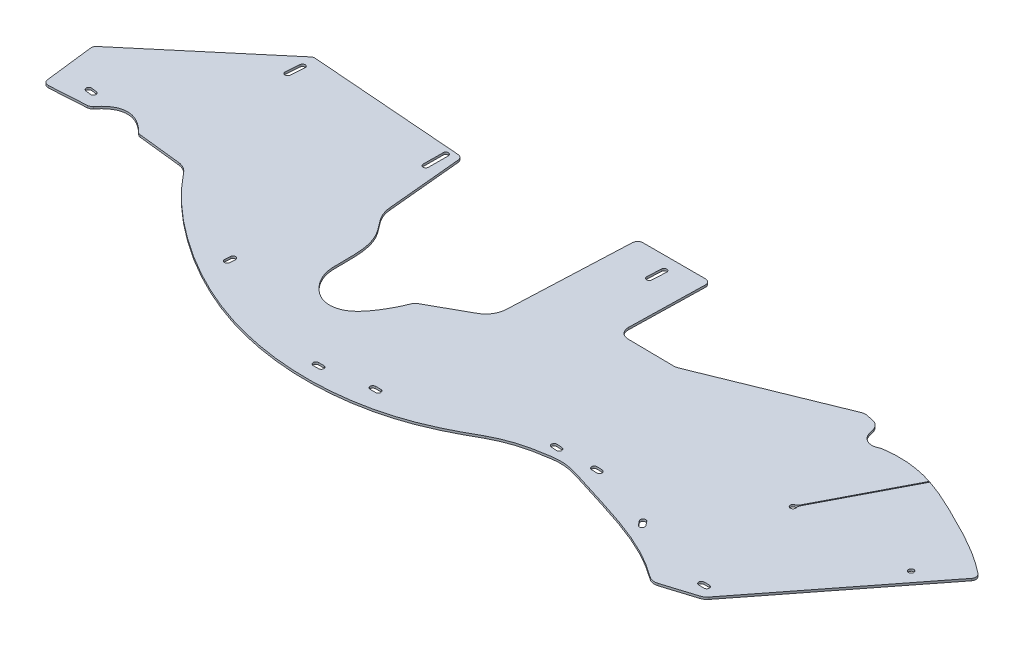
SolidWorks part; units mm, degrees
ref_plane "Front Plane" through (0, 0, 0) normal (0, 0, 1) x (1, 0, 0)
ref_plane "Top Plane" through (0, 0, 0) normal (0, 1, 0) x (1, 0, 0)
ref_plane "Right Plane" through (0, 0, 0) normal (1, 0, 0) x (0, 0, -1)
sketch "Sketch1" plane through (0, 0, 0) normal (0, 1, 0) x (1, 0, 0)
  line L0 (851.3584, -690.9266) -> (2338.9033, -2006.5335) construction
  line L1 (0, 0) -> (914.4, 0)
  line L2 (-5.3287, -153.1342) -> (131.8706, -37.3515)
  line L3 (136.4536, -35.8731) -> (319.5901, -49.9793)
  line L4 (325.4241, -55.712) -> (333.8869, -145.0824)
  line L5 (341.0028, -163.6309) -> (350.751, -176.7721)
  line L6 (-7.538, -158.7449) -> (-0.5962, -216.4972)
  line L7 (6.1047, -222.077) -> (49.5173, -219.3625)
  line L8 (111.0954, -218.2411) -> (162.3658, -223.8905)
  line L9 (878.7809, -371.8765) -> (916.7447, -360.0034)
  line L10 (922.964, -355.6982) -> (1059.3899, -180.9691)
  line L11 (600.276, -37.4685) -> (598.3017, -126.5968)
  line L12 (610.0599, -138.7632) -> (664.7501, -139.4182)
  line L13 (669.6781, -138.4869) -> (823.2965, -76.141)
  line L14 (830.7465, -75.4935) -> (838.6732, -77.2008)
  line L15 (848.1714, -85.9934) -> (850.3383, -93.2741)
  line L16 (448.4134, -227.3098) -> (494.4029, -201.6417)
  line L17 (507.4001, -180.5648) -> (513.6347, -37.0522)
  line L18 (519.9787, -30.9778) -> (593.9275, -30.9778)
  line L19 (34.0126, -202.2038) -> (40.3015, -203.0832) construction
  line L20 (34.4523, -199.0594) -> (40.7411, -199.9388)
  line L21 (33.573, -205.3482) -> (39.8618, -206.2276)
  line L22 (135.4768, -67.9225) -> (136.7875, -51.6134) construction
  line L23 (132.312, -67.6682) -> (133.6227, -51.359)
  line L24 (138.6416, -68.1769) -> (139.9523, -51.8677)
  line L25 (312.1521, -57.0309) -> (312.0105, -80.6873) construction
  line L26 (315.3271, -57.0499) -> (315.1854, -80.7063)
  line L27 (308.9772, -57.0118) -> (308.8355, -80.6683)
  line L28 (292.1635, -296.2194) -> (292.6086, -289.885) construction
  line L29 (288.9963, -295.9968) -> (289.4414, -289.6625)
  line L30 (295.3307, -296.4419) -> (295.7758, -290.1075)
  line L31 (450.5431, -349.5399) -> (456.8931, -349.5401) construction
  line L32 (450.5432, -346.3649) -> (456.8932, -346.3651)
  line L33 (450.5431, -352.7149) -> (456.8931, -352.7151)
  line L34 (508.8141, -340.1517) -> (515.1641, -340.1517) construction
  line L35 (508.8141, -336.9767) -> (515.1641, -336.9767)
  line L36 (508.8141, -343.3267) -> (515.1641, -343.3267)
  line L37 (675.6954, -292.0677) -> (682.0278, -292.54) construction
  line L38 (675.9315, -288.9015) -> (682.2639, -289.3738)
  line L39 (675.4592, -295.2339) -> (681.7916, -295.7062)
  line L40 (722.662, -291.3716) -> (729.0031, -291.7069) construction
  line L41 (722.8296, -288.201) -> (729.1708, -288.5363)
  line L42 (722.4943, -294.5422) -> (728.8355, -294.8775)
  line L43 (805.8956, -316.7947) -> (809.8059, -321.7979) construction
  line L44 (808.3972, -314.8396) -> (812.3075, -319.8428)
  line L45 (803.394, -318.7499) -> (807.3043, -323.7531)
  line L46 (904.6062, -346.3649) -> (910.9562, -346.3649) construction
  line L47 (904.6062, -343.1899) -> (910.9562, -343.1899)
  line L48 (904.6062, -349.5399) -> (910.9562, -349.5399)
  line L49 (560.224, -63.7474) -> (561.1068, -47.0434) construction
  line L50 (557.0534, -63.5799) -> (557.9362, -46.8758)
  line L51 (563.3946, -63.915) -> (564.2773, -47.2109)
  line L52 (883.5758, -207.7343) -> (935.9714, -106.7485)
  line L53 (882.6157, -206.9681) -> (934.8092, -106.372)
  line L54 (881.008, -210.0666) -> (882.0579, -210.6598) construction
  line L55 (881.5329, -210.3632) -> (879.9994, -213.0771) construction
  arc A1 (850.3383, -93.2741) -> (870.1301, -101.8845) centre (863.8577, -89.2504) ccw
  arc A2 (175.2485, -231.0039) -> (162.3658, -223.8905) centre (160.2703, -242.9077) ccw
  arc A3 (333.8869, -145.0824) -> (341.0028, -163.6309) centre (370.7079, -141.5956) ccw
  arc A4 (494.4029, -201.6417) -> (507.4001, -180.5648) centre (482.024, -179.4624) ccw
  arc A5 (598.3017, -126.5968) -> (610.0599, -138.7632) centre (610.2025, -126.8604) ccw
  arc A6 (664.7501, -139.4182) -> (669.6781, -138.4869) centre (664.9022, -126.7191) ccw
  arc A7 (878.7809, -371.8765) -> (867.4226, -369.9547) centre (874.99, -359.7554) cw
  arc A8 (916.7447, -360.0034) -> (922.964, -355.6982) centre (912.9538, -347.8824) ccw
  arc A9 (873.7509, -100.7225) -> (870.1301, -101.8845) centre (875.7775, -113.2598) ccw
  arc A10 (823.2965, -76.141) -> (830.7465, -75.4935) centre (828.0725, -87.9088) cw
  arc A11 (838.6732, -77.2008) -> (848.1714, -85.9934) centre (835.9991, -89.6161) cw
  arc A12 (1059.3899, -180.9691) -> (1058.3506, -172.1019) centre (1054.3849, -177.0612) ccw
  arc A13 (34.4523, -199.0594) -> (33.573, -205.3482) centre (34.0126, -202.2038) ccw
  arc A14 (39.8618, -206.2276) -> (40.7411, -199.9388) centre (40.3015, -203.0832) ccw
  arc A15 (132.312, -67.6682) -> (138.6416, -68.1769) centre (135.4768, -67.9225) ccw
  arc A16 (139.9523, -51.8677) -> (133.6227, -51.359) centre (136.7875, -51.6134) ccw
  arc A17 (315.3271, -57.0499) -> (308.9772, -57.0118) centre (312.1521, -57.0309) ccw
  arc A18 (308.8355, -80.6683) -> (315.1854, -80.7063) centre (312.0105, -80.6873) ccw
  arc A19 (288.9963, -295.9968) -> (295.3307, -296.4419) centre (292.1635, -296.2194) ccw
  arc A20 (295.7758, -290.1075) -> (289.4414, -289.6625) centre (292.6086, -289.885) ccw
  arc A21 (450.5432, -346.3649) -> (450.5431, -352.7149) centre (450.5431, -349.5399) ccw
  arc A22 (456.8931, -352.7151) -> (456.8932, -346.3651) centre (456.8931, -349.5401) ccw
  arc A23 (508.8141, -336.9767) -> (508.8141, -343.3267) centre (508.8141, -340.1517) ccw
  arc A24 (515.1641, -343.3267) -> (515.1641, -336.9767) centre (515.1641, -340.1517) ccw
  arc A25 (675.9315, -288.9015) -> (675.4592, -295.2339) centre (675.6954, -292.0677) ccw
  arc A26 (681.7916, -295.7062) -> (682.2639, -289.3738) centre (682.0278, -292.54) ccw
  arc A27 (722.8296, -288.201) -> (722.4943, -294.5422) centre (722.662, -291.3716) ccw
  arc A28 (728.8355, -294.8775) -> (729.1708, -288.5363) centre (729.0031, -291.7069) ccw
  arc A29 (808.3972, -314.8396) -> (803.394, -318.7499) centre (805.8956, -316.7947) ccw
  arc A30 (807.3043, -323.7531) -> (812.3075, -319.8428) centre (809.8059, -321.7979) ccw
  arc A31 (904.6062, -343.1899) -> (904.6062, -349.5399) centre (904.6062, -346.3649) ccw
  arc A32 (910.9562, -349.5399) -> (910.9562, -343.1899) centre (910.9562, -346.3649) ccw
  arc A33 (557.0534, -63.5799) -> (563.3946, -63.915) centre (560.224, -63.7474) ccw
  arc A34 (564.2773, -47.2109) -> (557.9362, -46.8758) centre (561.1068, -47.0434) ccw
  arc A35 (878.9926, -210.066) -> (883.0703, -212.271) centre (879.9994, -213.0771) ccw
  circle A36 centre (1016.0848, -209.0617) radius 3.175
  arc A37 (600.276, -37.4685) -> (593.9275, -30.9778) centre (593.9275, -37.3278) ccw
  arc A38 (513.6347, -37.0522) -> (519.9787, -30.9778) centre (519.9787, -37.3278) cw
  arc A39 (445.65, -230.4044) -> (448.4134, -227.3098) centre (451.5082, -232.8547) cw
  arc A40 (319.5901, -49.9793) -> (325.4241, -55.712) centre (319.1024, -56.3106) cw
  arc A41 (107.2877, -216.4064) -> (111.0954, -218.2411) centre (111.7908, -211.9293) ccw
  arc A42 (49.5173, -219.3625) -> (54.0607, -217.0152) centre (49.121, -213.0249) ccw
  arc A43 (-0.5962, -216.4972) -> (6.1047, -222.077) centre (5.7085, -215.7393) ccw
  arc A44 (-5.3287, -153.1342) -> (-7.538, -158.7449) centre (-1.2334, -157.9871) ccw
  arc A45 (131.8706, -37.3515) -> (136.4536, -35.8731) centre (135.9659, -42.2043) cw
  arc A46 (883.5758, -207.7343) -> (883.0703, -212.271) centre (889.2123, -210.6587) ccw
  arc A47 (882.6157, -206.9681) -> (878.9926, -210.066) centre (876.9792, -204.0436) cw
  spline S0 degree 3 poles (54.0607, -217.0152) (61.5062, -207.798) (70.9402, -202.0115) (88.8144, -201.9633) (99.0041, -208.0746) (107.2877, -216.4064) knots 0.031006 0.031006 0.031006 0.031006 0.441036 0.535227 0.972916 0.972916 0.972916 0.972916
  spline S1 degree 3 poles (873.7509, -100.7225) (892.0964, -97.7569) (912.9126, -99.7984) (932.4884, -105.6288) (934.8092, -106.372) knots 0.010512 0.010512 0.010512 0.010512 0.267872 0.302747 0.302747 0.302747 0.302747
  spline S2 degree 3 poles (867.4226, -369.9547) (846.2872, -354.2729) (800.4442, -332.5321) (742.2536, -316.1537) (700.4667, -302.0566) (673.1755, -306.5267) (649.18, -311.739) (630.6651, -319.7057) (625.0304, -322.9406) knots 0.023196 0.023196 0.023196 0.023196 0.311711 0.603247 0.708401 0.803326 0.906876 1 1 1 1
  spline S3 degree 3 poles (350.751, -176.7721) (361.254, -192.2578) (361.2248, -217.332) (360.8558, -250.3099) (372.4279, -270.2619) (390.7889, -282.4265) (413.7923, -279.58) (430.7044, -260.9382) (440.1809, -243.1342) (444.7919, -232.4559) (445.65, -230.4044) knots 0 0 0 0 0.266515 0.372222 0.489174 0.598377 0.68314 0.814057 0.95565 0.989066 0.989066 0.989066 0.989066
  spline S4 degree 3 poles (175.2485, -231.0039) (197.3803, -258.8516) (255.1104, -309.0868) (362.8525, -363.554) (474.694, -375.2218) (564.5582, -355.2544) (606.4867, -333.5868) (625.0304, -322.9406) knots 0 0 0 0 0.214414 0.45252 0.717397 0.871692 1 1 1 1
  spline S5 degree 3 poles (935.9714, -106.7485) (950.7325, -111.5857) (991.367, -130.8757) (1033.4128, -152.4397) (1057.1708, -171.1584) (1058.3506, -172.1019) knots 0.308575 0.308575 0.308575 0.308575 0.530873 0.946734 0.968622 0.968622 0.968622 0.968622
  point P9 (37.157, -202.6435)
  point P18 (608.9648, -331.6104)
  point P19 (400.1796, -365.0803)
  point P60 (667.3079, -139.4489)
  point P73 (136.1322, -59.768)
  point P86 (312.0813, -68.8591)
  point P95 (292.3861, -293.0522)
  point P102 (453.7181, -349.54)
  point P109 (511.9891, -340.1517)
  point P116 (678.8616, -292.3039)
  point P123 (725.8326, -291.5392)
  point P130 (807.8508, -319.2963)
  point P137 (907.7812, -346.3649)
  point P144 (560.6654, -55.3954)
  point P157 (600.4197, -30.9778)
  point P160 (513.8986, -30.9778)
  point P166 (324.9202, -50.3899)
  point P172 (0, 0)
  point P175 (0.1195, -222.4512)
  point P178 (-7.9468, -155.3436)
  point P181 (133.8592, -35.6733)
  point P190 (0, 0)
  point P191 (312.0105, -80.6873)
  point P192 (312.1045, -64.9861)
  point P193 (0, 0)
  point P194 (682.0278, -292.54)
  point P195 (0, 0)
  point P196 (456.8931, -349.5399)
  point P197 (508.8141, -340.1517)
  dimension "D2" = 12.7
  dimension "D3" = 12.7
  dimension "D4" = 6.35
  dimension "D5" = 6.35
  dimension "D6" = 3.175
  dimension "D7" = 6.35
  dimension "D8" = 6.35
  dimension "D1" = 914.4
  dimension "D9" = 6.35
extrude "Boss-Extrude1" add sketch "Sketch1" along normal blind 2.54 contours S5 L52 A46 A35 A47 L53 S1 A9 A1 L15 A11 L14 A10 L13 A6 L12 A5 L11 A37 L18 A38 L17 A4 L16 A39 S3 L5 A3 L4 A40 L3 A45 L2 A44 L6 A43 L7 A42 S0 A41 L8 A2 S4 S2 A7 L9 A8 L10 A12 A36
